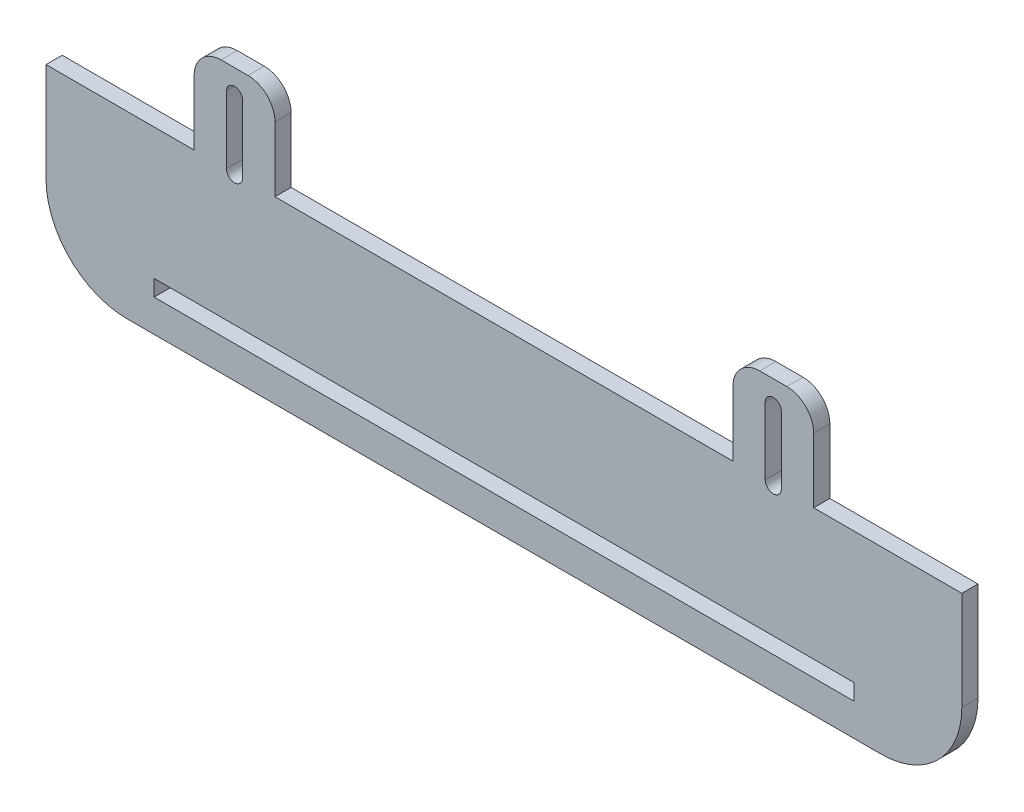
SolidWorks part; units mm, degrees
ref_plane "Front" through (0, 0, 0) normal (0, 0, 1) x (1, 0, 0)
ref_plane "Top" through (0, 0, 0) normal (0, 1, 0) x (1, 0, 0)
ref_plane "Right" through (0, 0, 0) normal (1, 0, 0) x (0, 0, -1)
sketch "Sketch1" plane through (0, 0, 0) normal (0, 0, 1) x (1, 0, 0)
  line L0 (-88.6222, -43.25) -> (-61.1222, -43.25)
  line L1 (53.8778, -43.25) -> (81.3778, -43.25)
  line L2 (-61.1222, -26.25) -> (-46.1222, -26.25)
  line L3 (-53.6222, -43.25) -> (-53.6222, -30.75) construction
  line L4 (-46.1222, -26.25) -> (-46.1222, -43.25)
  line L5 (-46.1222, -43.25) -> (38.8778, -43.25)
  line L6 (38.8778, -43.25) -> (38.8778, -26.25)
  line L7 (38.8778, -26.25) -> (53.8778, -26.25)
  line L8 (-55.1222, -43.25) -> (-55.1222, -30.75)
  line L9 (-52.1222, -43.25) -> (-52.1222, -30.75)
  line L10 (46.3778, -43.25) -> (46.3778, -30.75) construction
  line L11 (44.8778, -43.25) -> (44.8778, -30.75)
  line L12 (53.8778, -26.25) -> (53.8778, -43.25)
  line L13 (-61.1222, -26.25) -> (-61.1222, -43.25)
  line L14 (47.8778, -43.25) -> (47.8778, -30.75)
  line L15 (66.3778, -76.5985) -> (-73.6222, -76.5985)
  line L16 (-88.6222, -43.25) -> (-88.6222, -61.5985)
  line L17 (81.3778, -43.25) -> (81.3778, -61.5985)
  arc A0 (-73.6222, -76.5985) -> (-88.6222, -61.5985) centre (-73.6222, -61.5985) cw
  arc A1 (66.3778, -76.5985) -> (81.3778, -61.5985) centre (66.3778, -61.5985) ccw
  arc A4 (-55.1222, -43.25) -> (-52.1222, -43.25) centre (-53.6222, -43.25) ccw
  arc A5 (-52.1222, -30.75) -> (-55.1222, -30.75) centre (-53.6222, -30.75) ccw
  arc A6 (44.8778, -43.25) -> (47.8778, -43.25) centre (46.3778, -43.25) ccw
  arc A7 (47.8778, -30.75) -> (44.8778, -30.75) centre (46.3778, -30.75) ccw
  point P16 (-3.6222, -76.5985)
  point P17 (-88.6222, -76.5985)
  point P19 (-53.6222, -37)
  point P26 (46.3778, -37)
  point P32 (81.3778, -76.5985)
  dimension "D7" = 7.5
  dimension "D8" = 170
  dimension "D10" = 170
  dimension "D11" = 33.3485
  dimension "D12" = 15
  dimension "D13" = 12.5
  dimension "D14" = 12.5
  dimension "D17" = 27.5
  dimension "D19" = 1.5
  dimension "D2" = 27.5
  dimension "D3" = 15
  dimension "D4" = 15
  dimension "D5" = 17
  dimension "D6" = 17
  dimension "D9" = 7.5
extrude "Boss-Extrude1" add sketch "Sketch1" along normal blind 3
fillet "Fillet2" radius 5 4 edges at (38.8778, -26.25, 1.5) (53.8778, -26.25, 1.5) (-46.1222, -26.25, 1.5) (-61.1222, -26.25, 1.5)
sketch "Sketch2" plane through (0, 0, 3) normal (0, 0, 1) x (1, 0, 0)
  line L0 (-73.6222, -76.5985) -> (66.3778, -76.5985) construction
  line L1 (61.3153, -67.5985) -> (-68.5597, -67.5985)
  line L2 (61.3153, -67.5985) -> (61.3153, -70.5985)
  line L3 (61.3153, -70.5985) -> (-68.5597, -70.5985)
  line L4 (-68.5597, -67.5985) -> (-68.5597, -70.5985)
  line L5 (61.3153, -67.5985) -> (-68.5597, -70.5985) construction
  line L6 (61.3153, -70.5985) -> (-68.5597, -67.5985) construction
  point P0 (-3.6222, -69.0985)
  dimension "D1" = 6
  dimension "D2" = 3
extrude "Cut-Extrude1" cut sketch "Sketch2" against normal blind 10
